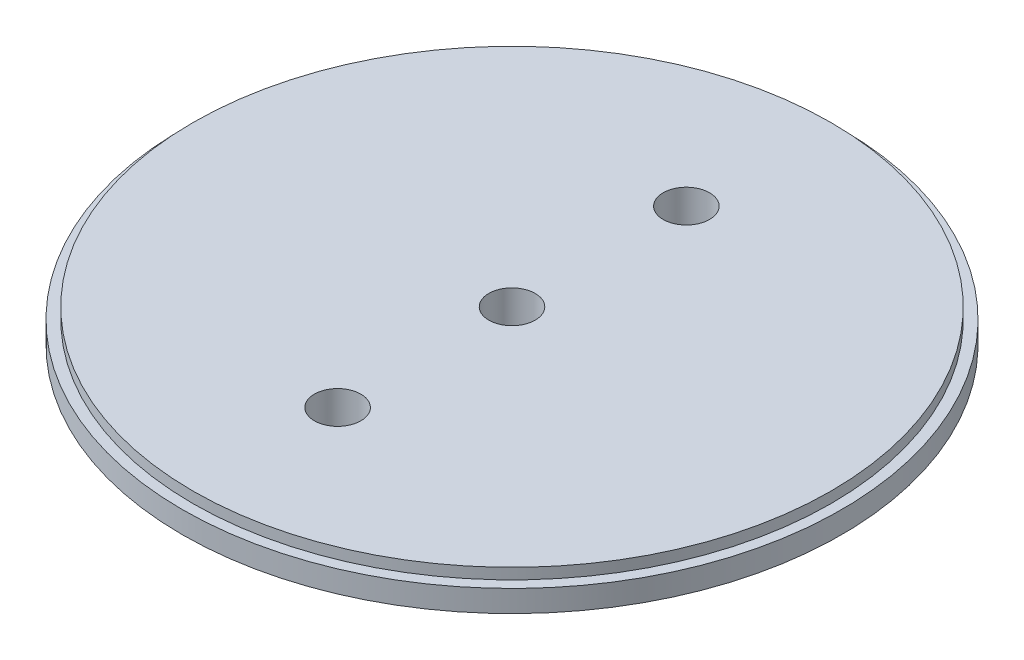
SolidWorks part; units mm, degrees
material "A-Glass Fiber"
ref_plane "Front Plane" through (0, 0, 0) normal (0, 0, 1) x (1, 0, 0)
ref_plane "Top Plane" through (0, 0, 0) normal (0, 1, 0) x (1, 0, 0)
ref_plane "Right Plane" through (0, 0, 0) normal (1, 0, 0) x (0, 0, -1)
sketch "Sketch1" plane through (0, 0, 0) normal (0, 1, 0) x (1, 0, 0)
  circle A0 centre (0, 0) radius 48.006
  dimension "D1" = 96.012
extrude "Boss-Extrude1" add sketch "Sketch1" along normal mid plane 3.175
sketch "Sketch2" plane through (0, 1.5875, 0) normal (0, 1, 0) x (1, 0, 0)
  circle A0 centre (0, 0) radius 46.482
  dimension "D1" = 92.964
extrude "Boss-Extrude2" add sketch "Sketch2" along normal mid plane 3.175
sketch "Sketch3" plane through (0, 3.175, 0) normal (0, 1, 0) x (1, 0, 0)
  point P0 (0, 0)
hole_wizard "1/4 Clearance Hole1" positions "Sketch3" profile "Sketch4" hole size "1/4" standard "ANSI Inch" end condition through all
sketch "Sketch4" plane through (0, 3.175, 0) normal (1, 0, 0) x (0, 0, 1)
  line L0 (0, 0) -> (0, 4.7625)
  line L1 (0, 4.7625) -> (3.3782, 4.7625)
  line L2 (3.3782, 4.7625) -> (3.3782, 0)
  line L5 (3.3782, 0) -> (0, 0)
  line L11 (0, -6.35) -> (0, 107.95) construction
  dimension "Thru Hole Dia." = 6.7564
  dimension "Thru Hole Depth" = 4.7625
sketch "Sketch5" plane through (0, -1.5875, 0) normal (0, -1, 0) x (1, 0, 0)
  line L0 (0, 25.4) -> (0, -25.4) construction
  dimension "D1" = 25.4
  dimension "D2" = 25.4
sketch "Sketch6" plane through (0, -1.5875, 0) normal (0, -1, 0) x (-1, 0, 0)
  point P0 (0, 25.4)
  point P3 (0, -25.4)
hole_wizard "1/4 Clearance Hole2" positions "Sketch6" profile "Sketch7" hole size "1/4" standard "ANSI Inch" end condition through all
sketch "Sketch7" plane through (0, -1.5875, -25.4) normal (1, 0, 0) x (0, 0, -1)
  line L0 (0, 0) -> (0, 4.7625)
  line L1 (0, 4.7625) -> (3.3782, 4.7625)
  line L2 (3.3782, 4.7625) -> (3.3782, 0)
  line L5 (3.3782, 0) -> (0, 0)
  line L11 (0, -6.35) -> (0, 107.95) construction
  dimension "Thru Hole Dia." = 6.7564
  dimension "Thru Hole Depth" = 4.7625
